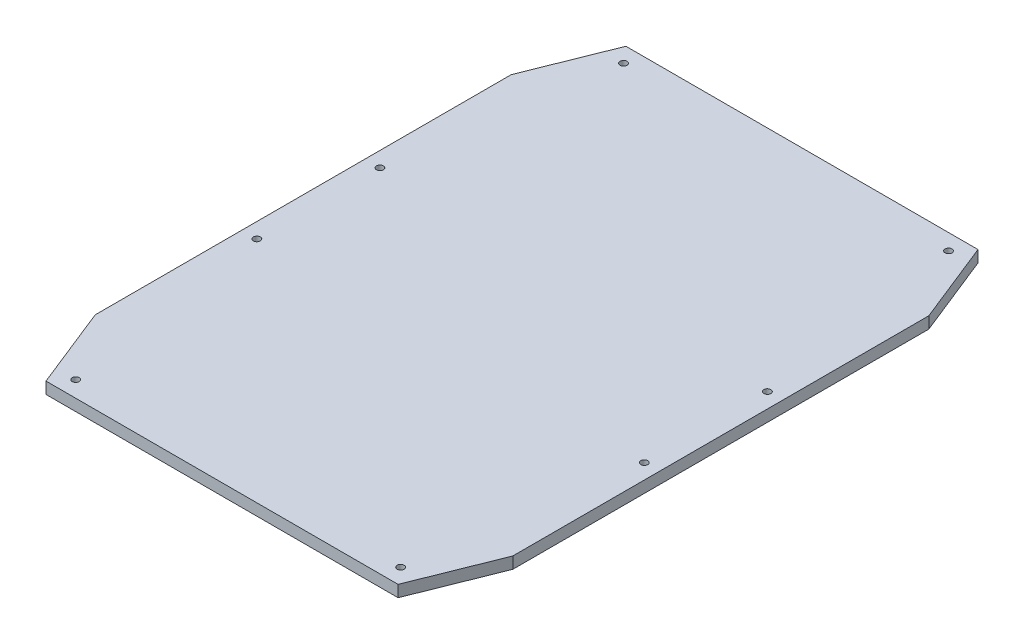
SolidWorks part; units mm, degrees
ref_plane "Front Plane" through (0, 0, 0) normal (0, 0, 1) x (1, 0, 0)
ref_plane "Top Plane" through (0, 0, 0) normal (0, 1, 0) x (1, 0, 0)
ref_plane "Right Plane" through (0, 0, 0) normal (1, 0, 0) x (0, 0, -1)
sketch "Sketch1" plane through (0, 0, 0) normal (0, 1, 0) x (1, 0, 0)
  line L0 (0, 0) -> (151.72, 0)
  line L1 (0, 0) -> (-14.1231, 35.3103)
  line L2 (-14.1231, 35.3103) -> (-14.1231, 214.6003)
  line L3 (-14.1231, 124.9553) -> (195.0525, 124.9553) construction
  line L4 (75.86, 0) -> (75.86, 282.4063) construction
  line L5 (0, 249.9106) -> (151.72, 249.9106)
  line L6 (0, 249.9106) -> (-14.1231, 214.6003)
  line L7 (151.72, 0) -> (165.8431, 35.3103)
  line L8 (151.72, 249.9106) -> (165.8431, 214.6003)
  line L9 (165.8431, 35.3103) -> (165.8431, 214.6003)
  dimension "D1" = 151.72
  dimension "D2" = 38.03
  dimension "D3" = 111.8
  dimension "D4" = 179.29
extrude "Boss-Extrude1" add sketch "Sketch1" along normal blind 5
sketch "Sketch2" plane through (0, 5, 0) normal (0, 1, 0) x (1, 0, 0)
  circle A0 centre (159.34, 98.4779) radius 1.5
  circle A1 centre (145.8834, 6.9521) radius 1.5
  circle A2 centre (5.8409, 6.9521) radius 1.5
  circle A3 centre (-7.6157, 98.4779) radius 1.5
  circle A4 centre (-7.6157, 151.5221) radius 1.5
  circle A5 centre (5.8409, 243.0479) radius 1.5
  circle A6 centre (145.8834, 243.0479) radius 1.5
  circle A7 centre (159.34, 151.5221) radius 1.5
extrude "Cut-Extrude1" cut sketch "Sketch2" against normal blind 10
